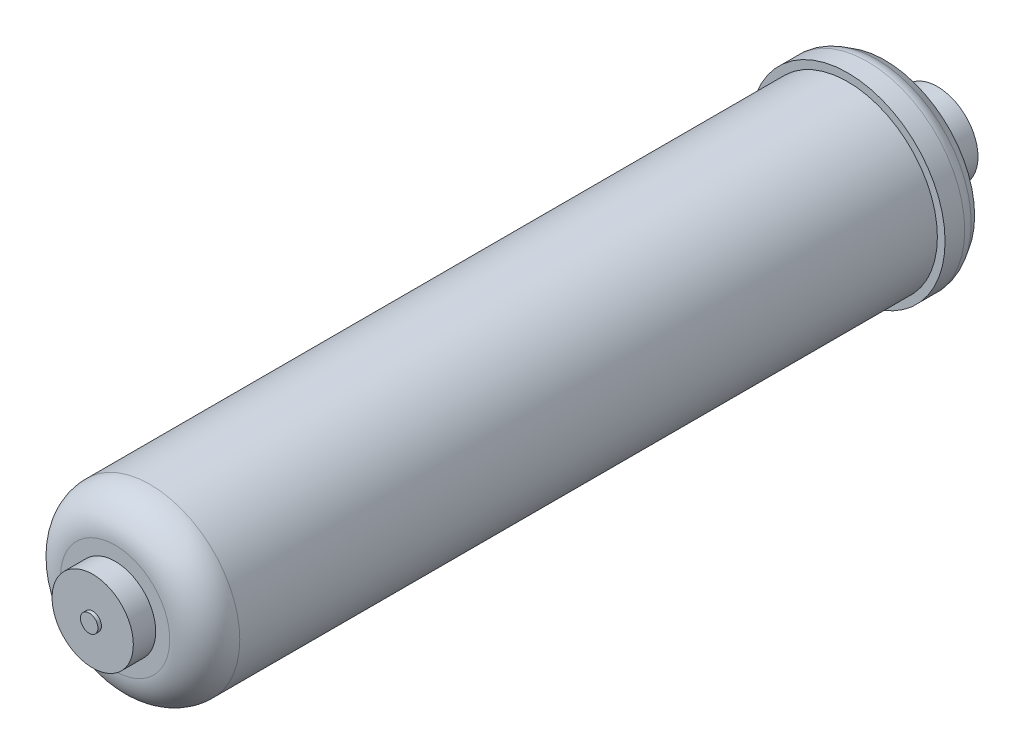
SolidWorks part; units mm, degrees
ref_plane "Front Plane" through (0, 0, 0) normal (0, 0, 1) x (1, 0, 0)
ref_plane "Top Plane" through (0, 0, 0) normal (0, 1, 0) x (1, 0, 0)
ref_plane "Right Plane" through (0, 0, 0) normal (1, 0, 0) x (0, 0, -1)
sketch "Sketch1" plane through (0, 0, 0) normal (1, 0, 0) x (0, 0, -1)
  line L0 (0, 0) -> (394.1281, 0) construction
  line L1 (0, 0) -> (0, 3.175)
  line L2 (0, 3.175) -> (1.27, 3.175)
  line L3 (1.27, 3.175) -> (1.27, 14.732)
  line L4 (1.27, 14.732) -> (9.398, 14.732)
  line L5 (9.398, 14.732) -> (9.398, 32.512)
  line L6 (9.398, 32.512) -> (275.082, 32.512)
  line L7 (275.082, 32.512) -> (275.082, 35.306)
  line L8 (275.082, 35.306) -> (283.972, 35.306)
  line L9 (283.972, 35.306) -> (288.544, 32.5551)
  line L10 (288.544, 32.5551) -> (299.466, 14.732)
  line L11 (299.466, 14.732) -> (307.594, 14.732)
  line L12 (307.594, 14.732) -> (307.594, 3.175)
  line L13 (307.594, 3.175) -> (308.864, 3.175)
  line L14 (308.864, 3.175) -> (308.864, 0)
  line L15 (0, 0) -> (308.864, 0)
  dimension "D1" = 1.27
  dimension "D2" = 6.35
  dimension "D3" = 8.128
  dimension "D4" = 65.024
  dimension "D5" = 70.612
  dimension "D6" = 4.572
  dimension "D7" = 10.922
  dimension "D8" = 273.812
  dimension "D9" = 306.324
  dimension "D10" = 29.464
  dimension "D11" = 29.464
  dimension "D12" = 121.5
revolve "Revolve1" add sketch "Sketch1" angle 360 about L0
fillet "Fillet1" radius 12.7 1 edges at (32.512, 0, -9.398)
fillet "Fillet2" radius 6.35 1 edges at (35.306, 0, -283.972)
